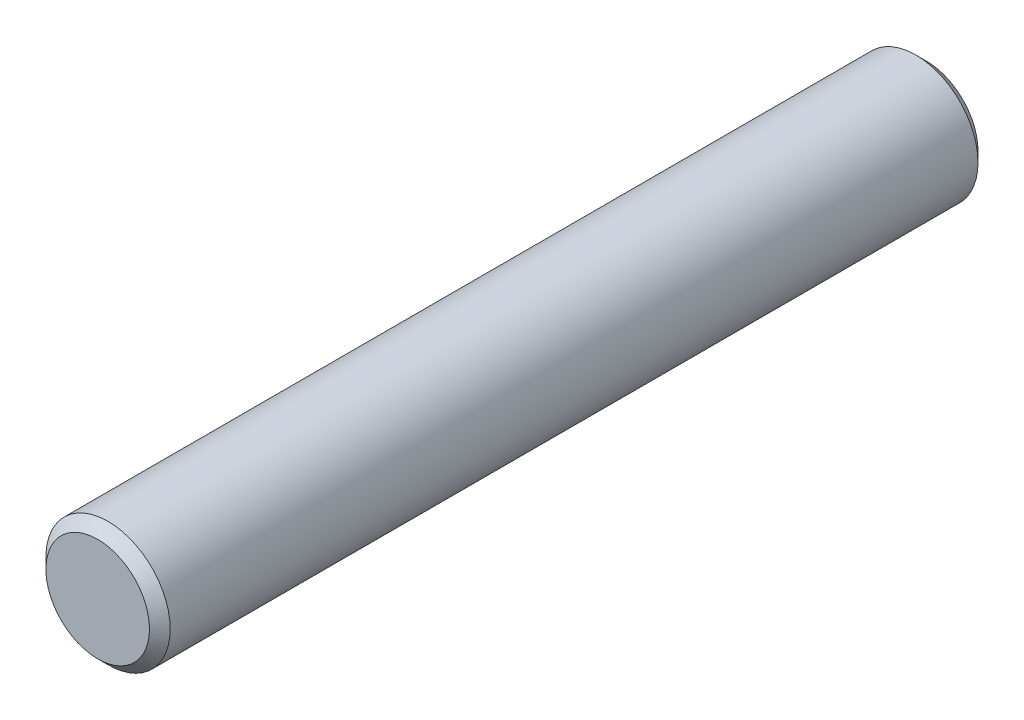
SolidWorks part; units mm, degrees
material "1.4310 (X10CrNi18-8)"
ref_plane "Front Plane" through (0, 0, 0) normal (0, 0, 1) x (1, 0, 0)
ref_plane "Top Plane" through (0, 0, 0) normal (0, 1, 0) x (1, 0, 0)
ref_plane "Right Plane" through (0, 0, 0) normal (1, 0, 0) x (0, 0, -1)
sketch "Sketch1" plane through (0, 0, 0) normal (0, 0, 1) x (1, 0, 0)
  circle A0 centre (0, 0) radius 1.5
  dimension "D1" = 3
extrude "Boss-Extrude1" add sketch "Sketch1" along normal mid plane 20
chamfer "Chamfer2" distance 0.25 angle 45 2 edges at (1.5, 0, -10) (1.5, 0, 10)
